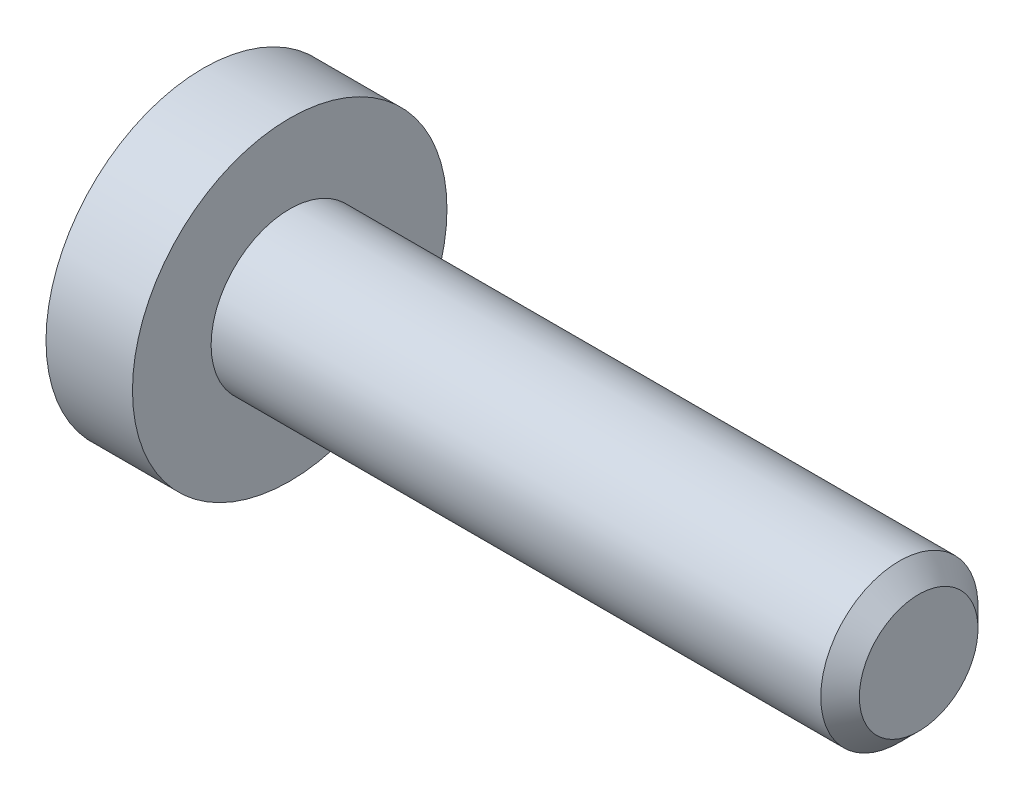
SolidWorks part; units mm, degrees
material "AISI 304"
ref_plane "正面" through (0, 0, 0) normal (0, 0, 1) x (1, 0, 0)
ref_plane "平面" through (0, 0, 0) normal (0, 1, 0) x (1, 0, 0)
ref_plane "右側面" through (0, 0, 0) normal (1, 0, 0) x (0, 0, -1)
ref_plane "Plane1" through (0, 0, 0) normal (0, 0, 1) x (1, 0, 0)
sketch "Sketch1" plane through (0, 0, 0) normal (0, 0, 1) x (1, 0, 0)
  line L0 (-1.1, 0) -> (-1.1, 2)
  line L1 (-1.1, 2) -> (0, 2)
  line L2 (0, 2) -> (0, 1)
  line L3 (0, 1) -> (7.7545, 1)
  line L4 (7.7545, 1) -> (8, 0.7545)
  line L5 (8, 0.7545) -> (8, 0)
  line L6 (8, 0) -> (-1.1, 0)
  line L7 (8, 0) -> (-1.1, 0) construction
revolve "Revolve1" add sketch "Sketch1" angle 360 about L7
cosmetic thread "Cosmetic Thread1" parameters "D1"=5.5748, "D2"=1.509
ref_plane "Plane2" through (-1.1, 0, 0) normal (1, 0, 0) x (0, 0, -1)
sketch "Sketch2" plane through (-1.1, 0, 0) normal (1, 0, 0) x (0, 0, -1)
  line L0 (-0.65, -0.3753) -> (0, -0.7506)
  line L1 (0, -0.7506) -> (0.65, -0.3753)
  line L2 (0.65, -0.3753) -> (0.65, 0.3753)
  line L3 (0.65, 0.3753) -> (0, 0.7506)
  line L4 (0, 0.7506) -> (-0.65, 0.3753)
  line L5 (-0.65, 0.3753) -> (-0.65, -0.3753)
extrude "Cut-Extrude1" cut sketch "Sketch2" along normal blind 1.2
